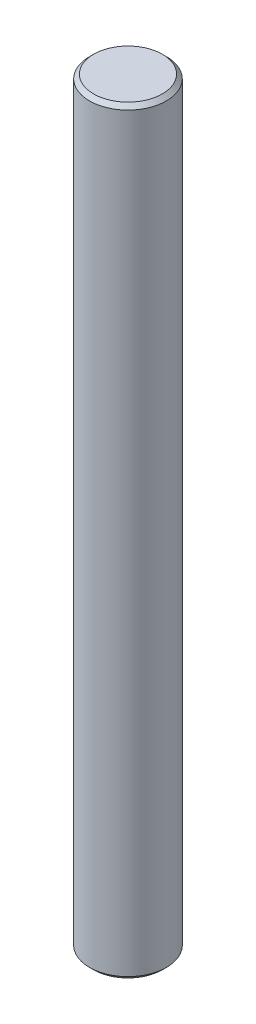
SolidWorks part; units mm, degrees
ref_plane "Front Plane" through (0, 0, 0) normal (0, 0, 1) x (1, 0, 0)
ref_plane "Top Plane" through (0, 0, 0) normal (0, 1, 0) x (1, 0, 0)
ref_plane "Right Plane" through (0, 0, 0) normal (1, 0, 0) x (0, 0, -1)
sketch "Sketch2" plane through (0, 0, 0) normal (0, 1, 0) x (1, 0, 0)
  circle A0 centre (0, 0) radius 4.826
  dimension "D1" = 9.652
extrude "Boss-Extrude1" add sketch "Sketch2" along normal mid plane 95.25
chamfer "Chamfer1" distance 0.508 angle 45 2 edges at (0, -47.625, 4.826) (0, 47.625, 4.826)
